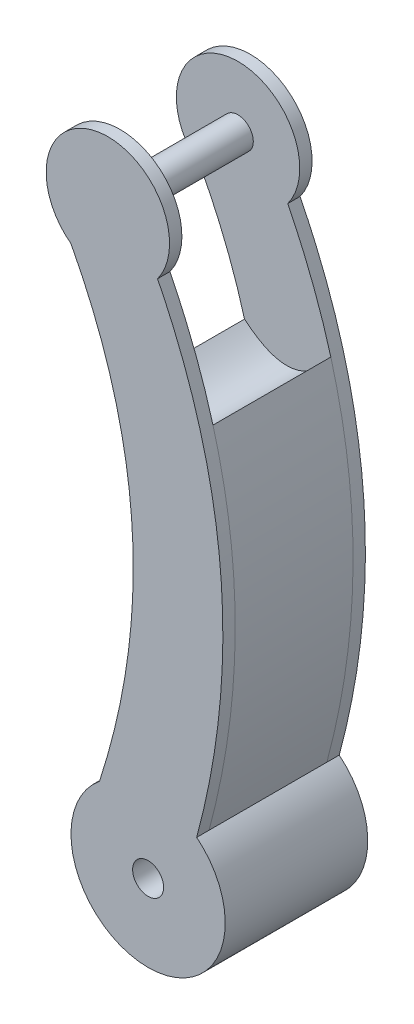
SolidWorks part; units mm, degrees
ref_plane "Front Plane" through (0, 0, 0) normal (0, 0, 1) x (1, 0, 0)
ref_plane "Top Plane" through (0, 0, 0) normal (0, 1, 0) x (1, 0, 0)
ref_plane "Right Plane" through (0, 0, 0) normal (1, 0, 0) x (0, 0, -1)
sketch "Sketch1" plane through (0, 0, 0) normal (0, 0, 1) x (1, 0, 0)
  circle A0 centre (0, 0) radius 25
  circle A1 centre (-13.0474, 181.7452) radius 20
  spline S0 degree 2 poles (15.7524, 19.4129) (37.6301, 100.7411) (3.0618, 169.8922) knots 0 0 0 1 1 1
  spline S1 degree 2 poles (-15.7524, 19.4129) (10.0324, 99.2405) (-25, 165.7098) knots 0 0 0 1 1 1
extrude "Boss-Extrude1" add sketch "Sketch1" along normal blind 4 contours A1 | S1 A0 S0 A1 | A0
sketch "Sketch4" plane through (0, 0, 4) normal (0, 0, 1) x (1, 0, 0)
  arc A2 (3.0618, 169.8922) -> (-25, 165.7098) centre (-13.0474, 181.7452) ccw
  arc A3 (-15.7524, 19.4129) -> (15.7524, 19.4129) centre (0, 0) ccw
  arc A5 (-15.7524, 19.4129) -> (15.7524, 19.4129) centre (0, 0) ccw
  parabola Q0 (-15.7524, 19.4129) -> (-25, 165.7098) focus (-91.0979, 103.6518) apex (-8.7913, 121.7302) construction
  parabola Q1 (15.7524, 19.4129) -> (3.0618, 169.8922) focus (-75.1175, 102.0594) apex (19.8139, 122.5388) construction
  parabola Q4 (-25, 165.7098) -> (-15.7524, 19.4129) focus (-91.0979, 103.6518) apex (-8.7913, 121.7302)
  parabola Q5 (15.7524, 19.4129) -> (3.0618, 169.8922) focus (-75.1175, 102.0594) apex (19.8139, 122.5388)
  parabola Q6 (-10.9531, 130.4559) -> (-15.7524, 19.4129) focus (-91.0979, 103.6518) apex (-8.7913, 121.7302)
  parabola Q7 (15.7524, 19.4129) -> (17.0319, 133.7951) focus (-75.1175, 102.0594) apex (19.8139, 122.5388)
  spline S0 degree 2 poles (-10.9531, 130.4559) (5.5646, 116.5405) (17.0319, 133.7951) knots 0 0 0 1 1 1
  dimension "D1" = 0
extrude "Boss-Extrude2" add sketch "Sketch4" along normal blind 19.1
mirror "Mirror18" about plane through (4.302, 124.333, 23.1) normal (0, 0, -1) of bodies 102 101
sketch "Sketch5" plane through (0, 0, 46.2) normal (0, 0, 1) x (1, 0, 0)
  circle A0 centre (0, 0) radius 5.02
extrude "Cut-Extrude1" cut sketch "Sketch5" against normal blind 49.2
sketch "Sketch7" plane through (0, 0, 4) normal (0, 0, 1) x (1, 0, 0)
  circle A3 centre (-13.1041, 181.7418) radius 5
extrude "Boss-Extrude4" add sketch "Sketch7" along normal blind 40.2 and the other way blind 2.2
